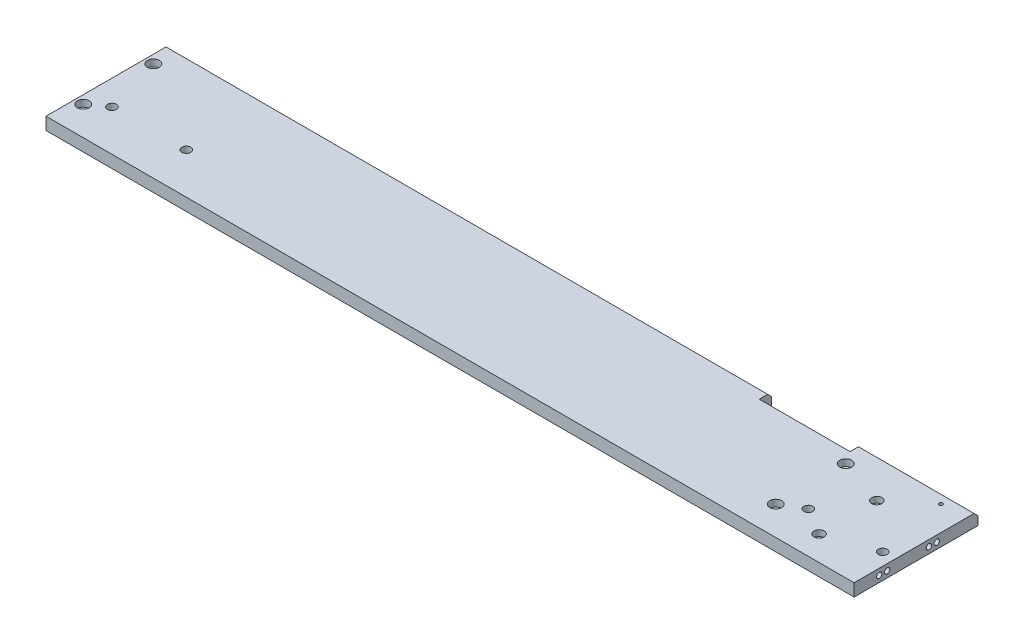
SolidWorks part; units mm, degrees
material "1060 Alloy"
ref_plane "Front Plane" through (0, 0, 0) normal (0, 0, 1) x (1, 0, 0)
ref_plane "Top Plane" through (0, 0, 0) normal (0, 1, 0) x (1, 0, 0)
ref_plane "Right Plane" through (0, 0, 0) normal (1, 0, 0) x (0, 0, -1)
sketch "Sketch1" plane through (0, 0, 0) normal (0, 1, 0) x (1, 0, 0)
  line L0 (532.64, 0) -> (621.59, 0)
  line L1 (0, 0) -> (462.84, 0)
  line L2 (0, 0) -> (0, -95.3)
  line L3 (0, -95.3) -> (621.59, -95.3)
  line L4 (621.59, 0) -> (621.59, -95.3)
  line L5 (462.84, 0) -> (532.64, 0) construction
  line L6 (462.84, 0) -> (462.84, -9.5)
  line L7 (462.84, -9.5) -> (532.64, -9.5)
  line L8 (532.64, 0) -> (532.64, -9.5)
  dimension "D1" = 621.59
  dimension "D2" = 95.3
  dimension "D3" = 88.95
  dimension "D4" = 69.8
  dimension "D5" = 9.5
extrude "Boss-Extrude1" add sketch "Sketch1" along normal blind 9.55
chamfer "Chamfer1" distance 3 angle 45 2 edges at (231.42, 9.55, 0) (577.115, 9.55, 0)
sketch "Sketch2" plane through (0, 9.55, 0) normal (0, 1, 0) x (-1, 0, 0)
  line L0 (-575.61, 76.28) -> (-575.61, 31.84) construction
  line L1 (-611.995, 63.695) -> (-554.785, 63.695) construction
  line L2 (-539.07, 19.16) -> (-539.07, 73.05) construction
  line L3 (-6.42, 19.16) -> (-6.42, 73.05) construction
  line L4 (-19.135, 63.695) -> (-76.345, 63.695) construction
  line L5 (-19.135, 67.14) -> (-19.135, 95.3) construction
  line L6 (0, 95.3) -> (-621.59, 95.3) construction
  line L7 (-15.69, 63.695) -> (0, 63.695) construction
  line L8 (0, 3) -> (0, 95.3) construction
  line L9 (-6.42, 77.66) -> (-6.42, 95.3) construction
  line L10 (-1.81, 73.05) -> (0, 73.05) construction
  line L11 (-539.07, 73.05) -> (-6.42, 73.05) construction
  line L12 (-539.07, 19.16) -> (-6.42, 19.16) construction
  line L13 (-543.68, 73.05) -> (-621.59, 73.05) construction
  line L14 (-621.59, 95.3) -> (-621.59, 3) construction
  line L15 (-602.545, 9.5) -> (-602.545, 3) construction
  line L16 (-621.59, 3) -> (-532.64, 3) construction
  line L17 (-603.93, 9.5) -> (-621.59, 9.5) construction
  line L18 (-615.44, 63.695) -> (-621.59, 63.695) construction
  line L19 (-579.59, 76.28) -> (-621.59, 76.28) construction
  line L20 (-575.61, 80.26) -> (-575.61, 95.3) construction
  circle A0 centre (-6.42, 19.16) radius 4.61 construction
  circle A1 centre (-6.42, 73.05) radius 4.61 construction
  circle A2 centre (-19.135, 63.695) radius 3.445 construction
  circle A3 centre (-76.345, 63.695) radius 3.445 construction
  circle A4 centre (-611.995, 63.695) radius 2.565
  circle A5 centre (-575.61, 31.84) radius 3.98 construction
  circle A6 centre (-575.61, 76.28) radius 3.98 construction
  circle A7 centre (-554.785, 63.695) radius 3.445
  circle A8 centre (-539.07, 19.16) radius 4.61 construction
  circle A9 centre (-539.07, 73.05) radius 4.61 construction
  circle A10 centre (-6.42, 19.16) radius 2.795
  circle A11 centre (-6.42, 73.05) radius 2.795
  circle A12 centre (-575.61, 76.28) radius 2.48
  circle A13 centre (-575.61, 31.84) radius 2.48
  circle A14 centre (-539.07, 73.05) radius 2.795
  circle A15 centre (-539.07, 19.16) radius 2.795
  circle A16 centre (-19.135, 63.695) radius 2.565
  circle A17 centre (-76.345, 63.695) radius 2.565
  circle A18 centre (-611.995, 63.695) radius 3.445 construction
  circle A19 centre (-602.545, 9.5) radius 1.385
  dimension "D1" = 5.59
  dimension "D2" = 9.22
  dimension "D7" = 6.89
  dimension "D8" = 5.13
  dimension "D12" = 7.96
  dimension "D13" = 4.96
  dimension "D14" = 2.77
  dimension "D3" = 17.64
  dimension "D4" = 1.81
  dimension "D5" = 53.89
  dimension "D6" = 15.69
  dimension "D9" = 28.16
  dimension "D10" = 57.21
  dimension "D11" = 77.91
  dimension "D15" = 6.5
  dimension "D16" = 17.66
  dimension "D17" = 6.15
  dimension "D18" = 42
  dimension "D19" = 44.44
  dimension "D20" = 15.04
extrude "Cut-Extrude1" cut sketch "Sketch2" against normal up to next
sketch "Sketch3" plane through (0, 9.55, 0) normal (0, 1, 0) x (-1, 0, 0)
  circle A0 centre (-6.42, 19.16) radius 4.61
  circle A1 centre (-6.42, 73.05) radius 4.61
  circle A2 centre (-539.07, 19.16) radius 4.61
  circle A3 centre (-539.07, 73.05) radius 4.61
  circle A4 centre (-6.42, 19.16) radius 4.61 construction
  circle A5 centre (-6.42, 73.05) radius 4.61 construction
  circle A7 centre (-539.07, 19.16) radius 4.61 construction
  circle A8 centre (-539.07, 73.05) radius 4.61 construction
extrude "Cut-Extrude2" cut sketch "Sketch3" against normal blind 5.2
sketch "Sketch4" plane through (0, 9.55, 0) normal (0, 1, 0) x (-1, 0, 0)
  circle A0 centre (-575.61, 31.84) radius 3.98 construction
  circle A1 centre (-575.61, 76.28) radius 3.98 construction
  circle A2 centre (-575.61, 31.84) radius 3.98
  circle A3 centre (-575.61, 76.28) radius 3.98
extrude "Cut-Extrude3" cut sketch "Sketch4" against normal blind 4.54
sketch "Sketch5" plane through (0, 9.55, 0) normal (0, 1, 0) x (-1, 0, 0)
  circle A0 centre (-611.995, 63.695) radius 3.445
  circle A1 centre (-76.345, 63.695) radius 3.445
  circle A2 centre (-19.135, 63.695) radius 3.445
  circle A4 centre (-611.995, 63.695) radius 3.445 construction
  circle A5 centre (-19.135, 63.695) radius 3.445 construction
  circle A6 centre (-76.345, 63.695) radius 3.445 construction
extrude "Cut-Extrude4" cut sketch "Sketch5" against normal blind 7.68
sketch "Sketch6" plane through (0, 0, 0) normal (0, -1, 0) x (1, 0, 0)
  circle A0 centre (611.995, 63.695) radius 4
  circle A1 centre (611.995, 63.695) radius 2.565
  circle A2 centre (76.345, 63.695) radius 4
  circle A3 centre (76.345, 63.695) radius 2.565
  circle A4 centre (19.135, 63.695) radius 4
  circle A5 centre (19.135, 63.695) radius 2.565
  circle A7 centre (611.995, 63.695) radius 2.565 construction
  circle A9 centre (76.345, 63.695) radius 2.565 construction
  circle A11 centre (19.135, 63.695) radius 2.565 construction
  dimension "D1" = 8
extrude "Boss-Extrude2" add sketch "Sketch6" along normal blind 2.5
sketch "Sketch7" plane through (0, 0, 9.5) normal (0, 0, -1) x (-1, 0, 0)
  line L0 (-507.305, 4.775) -> (-475.355, 4.775) construction
  line L1 (-532.64, 9.55) -> (-462.84, 9.55) construction
  line L2 (-532.64, 0) -> (-462.84, 0) construction
  line L3 (-505.24, 4.775) -> (-505.24, 0) construction
  line L4 (-477.42, 4.775) -> (-477.42, 0) construction
  line L5 (-532.64, 9.55) -> (-532.64, 0) construction
  circle A0 centre (-507.305, 4.775) radius 2.065
  circle A1 centre (-475.355, 4.775) radius 2.065
  dimension "D1" = 4.13
  dimension "D2" = 27.82
  dimension "D3" = 27.4
extrude "Cut-Extrude5" cut sketch "Sketch7" against normal blind 18.99
sketch "Sketch8" plane through (621.59, 0, 0) normal (1, 0, 0) x (0, 0, -1)
  line L0 (-75.935, 4.775) -> (-31.685, 4.775) construction
  line L1 (-95.3, 0) -> (0, 0) construction
  line L2 (-95.3, 9.55) -> (-3, 9.55) construction
  line L3 (-53.81, 4.775) -> (-53.81, 8.9098) construction
  line L4 (-29.62, 4.775) -> (0, 4.775) construction
  line L5 (0, 6.55) -> (0, 0) construction
  line L6 (-95.3, 4.775) -> (-78, 4.775) construction
  line L7 (-95.3, 9.55) -> (-95.3, 0) construction
  circle A0 centre (-31.685, 4.775) radius 2.065
  circle A1 centre (-37.755, 4.775) radius 2.065
  circle A2 centre (-69.865, 4.775) radius 2.065
  circle A3 centre (-75.935, 4.775) radius 2.065
  dimension "D1" = 4.13
  dimension "D2" = 17.3
  dimension "D3" = 6.07
  dimension "D4" = 29.62
extrude "Cut-Extrude6" cut sketch "Sketch8" against normal blind 18.7
